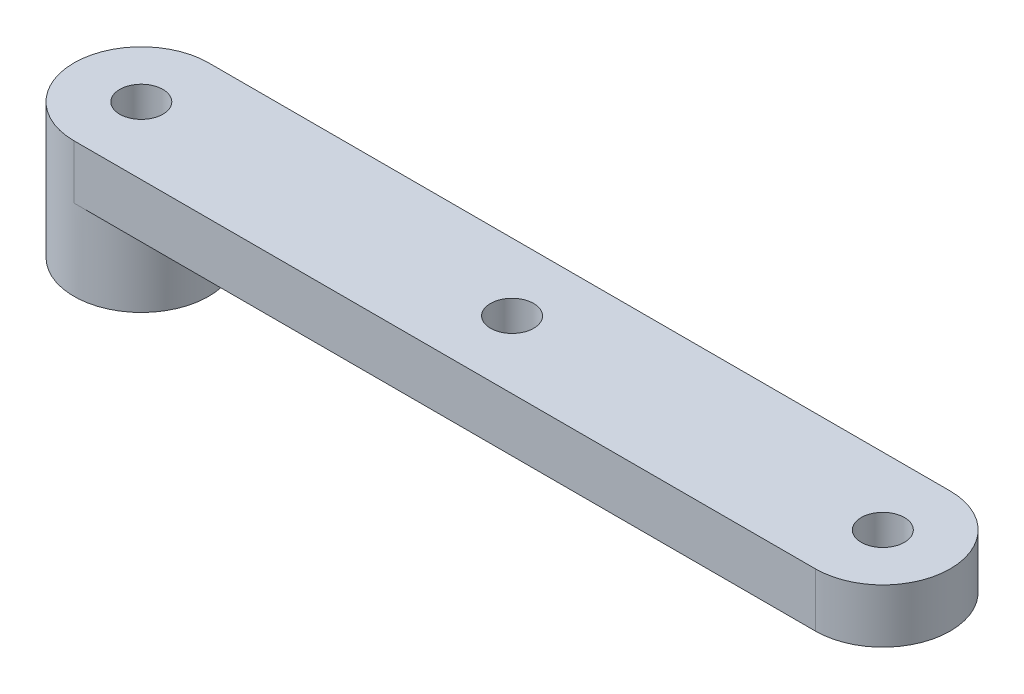
SolidWorks part; units mm, degrees
ref_plane "Front Plane" through (0, 0, 0) normal (0, 0, 1) x (1, 0, 0)
ref_plane "Top Plane" through (0, 0, 0) normal (0, 1, 0) x (1, 0, 0)
ref_plane "Right Plane" through (0, 0, 0) normal (1, 0, 0) x (0, 0, -1)
sketch "Sketch1" plane through (0, 0, 0) normal (0, 1, 0) x (1, 0, 0)
  line L0 (0, 0) -> (55, 0) construction
  line L1 (0, 5) -> (55, 5)
  line L2 (0, -5) -> (55, -5)
  arc A0 (0, 5) -> (0, -5) centre (0, 0) ccw
  arc A1 (55, -5) -> (55, 5) centre (55, 0) ccw
  point P3 (27.5, 0)
  dimension "D1" = 55
  dimension "D2" = 10
extrude "Boss-Extrude1" add sketch "Sketch1" along normal blind 4
sketch "Sketch2" plane through (0, 4, 0) normal (0, 1, 0) x (1, 0, 0)
  circle A0 centre (0, 0) radius 1.6
  circle A1 centre (27.5, 0) radius 1.6
  circle A2 centre (55, 0) radius 1.6
  dimension "D1" = 3.2
  dimension "D2" = 3.2
  dimension "D3" = 3.2
  dimension "D4" = 27.5
  dimension "D5" = 27.5
extrude "Cut-Extrude1" cut sketch "Sketch2" against normal through all
sketch "Sketch3" plane through (0, 0, 0) normal (0, -1, 0) x (1, 0, 0)
  circle A0 centre (0, 0) radius 5
extrude "Boss-Extrude2" add sketch "Sketch3" along normal blind 6
sketch "Sketch5" plane through (0, -6, 0) normal (0, -1, 0) x (1, 0, 0)
  circle A0 centre (0, 0) radius 1.6
  dimension "D1" = 3.2
extrude "Cut-Extrude2" cut sketch "Sketch5" against normal blind 6
